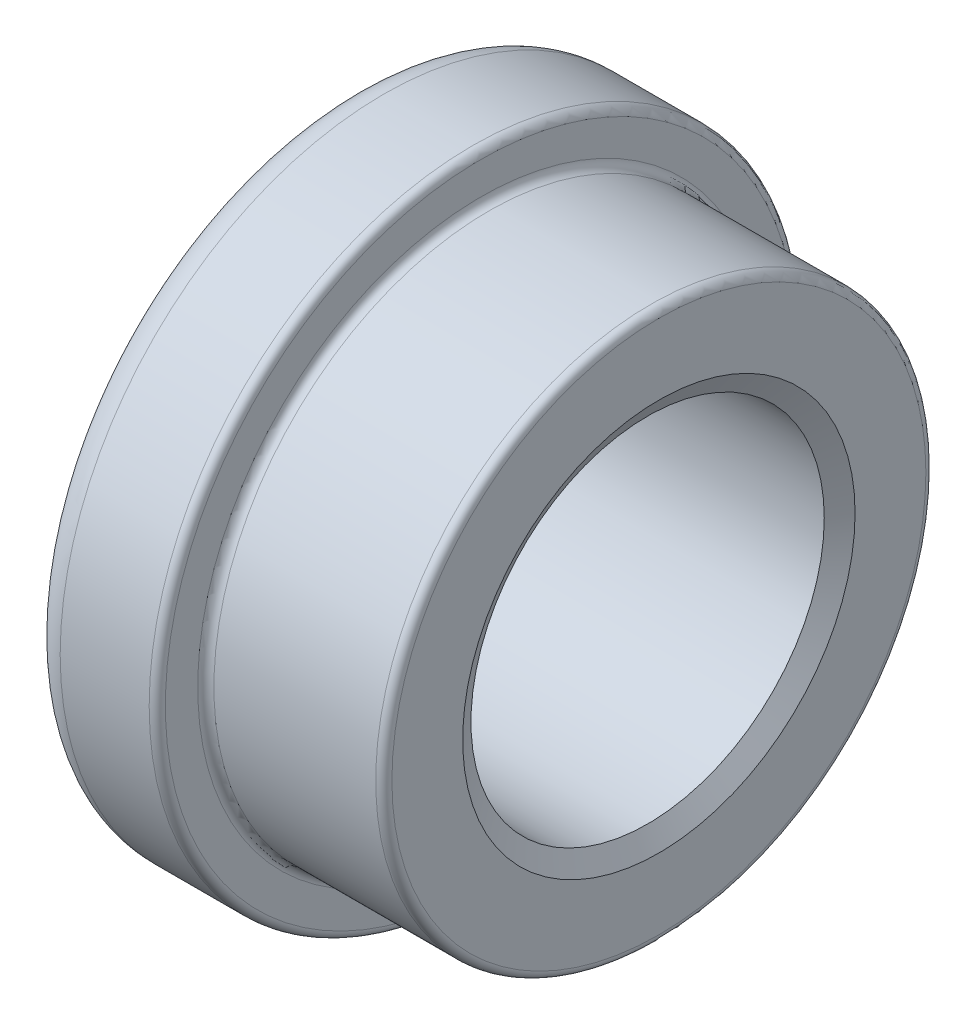
SolidWorks part; units mm, degrees
ref_plane "Plane1" through (0, 0, 0) normal (0, 0, 1) x (1, 0, 0)
ref_plane "Plane2" through (0, 0, 0) normal (0, 1, 0) x (1, 0, 0)
ref_plane "Plane3" through (0, 0, 0) normal (1, 0, 0) x (0, 0, -1)
sketch "Sketch1" plane through (0, 0, 0) normal (0, 0, 1) x (1, 0, 0)
  line L0 (0, 12.125) -> (0, 16.5)
  line L1 (-0.5, 17) -> (-10.5, 17)
  line L2 (-19, 18) -> (-19, 12.125)
  line L3 (-19, 12.125) -> (-18.3028, 10.9175)
  line L4 (-0.6972, 10.9175) -> (0, 12.125)
  line L5 (-11, 17.5) -> (-11, 19.5)
  line L6 (-11.5, 20) -> (-17, 20)
  line L12 (-18.3028, 10.9175) -> (-0.6972, 10.9175)
  line L13 (0, 0) -> (-20, 0) construction
  arc A0 (-17, 20) -> (-19, 18) centre (-17, 18) ccw
  arc A1 (-10.5, 17) -> (-11, 17.5) centre (-10.5, 17.5) cw
  arc A2 (-11.5, 20) -> (-11, 19.5) centre (-11.5, 19.5) cw
  arc A3 (-0.5, 17) -> (0, 16.5) centre (-0.5, 16.5) cw
  point P0 (0, 10.9175)
  point P12 (-19, 10.9175)
  dimension "D5" = 2
  dimension "D11" = 0.5
  dimension "D2" = 30
  dimension "D3" = 34
  dimension "D4" = 21.835
  dimension "D6" = 24.25
  dimension "D8" = 19
  dimension "D9" = 11
  dimension "D10" = 40
  dimension "D12" = 24.25
  dimension "30" = 30
revolve "Base-Revolve" add sketch "Sketch1" angle 360 about L13
cosmetic thread "Cosmetic Thread1" parameters "D2"=24
